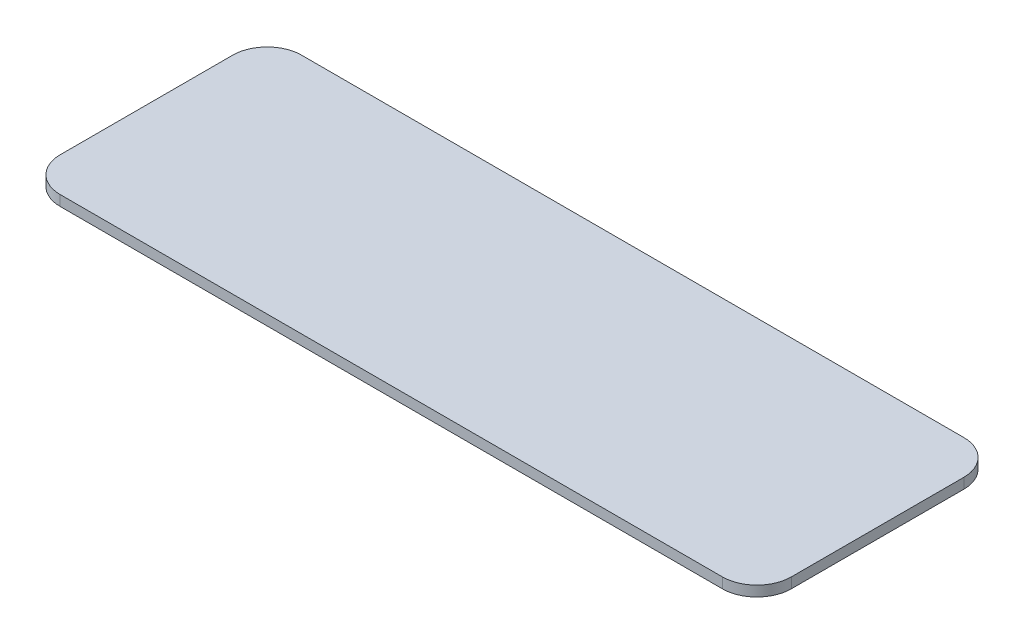
SolidWorks part; units mm, degrees
ref_plane "Front Plane" through (0, 0, 0) normal (0, 0, 1) x (1, 0, 0)
ref_plane "Top Plane" through (0, 0, 0) normal (0, 1, 0) x (1, 0, 0)
ref_plane "Right Plane" through (0, 0, 0) normal (1, 0, 0) x (0, 0, -1)
sketch "Sketch1" plane through (0, 0, 0) normal (0, 1, 0) x (1, 0, 0)
  line L1 (-106, -35) -> (106, -35)
  line L2 (-106, -35) -> (-106, 35)
  line L3 (-106, 35) -> (106, 35)
  line L4 (106, -35) -> (106, 35)
  line L5 (-106, -35) -> (106, 35) construction
  line L6 (-106, 35) -> (106, -35) construction
  point P0 (0, 0)
  dimension "D1" = 70
  dimension "D2" = 212
extrude "Boss-Extrude1" add sketch "Sketch1" along normal blind 3
fillet "Fillet1" radius 10 4 edges at (-106, 1.5, 35) (106, 1.5, 35) (106, 1.5, -35) (-106, 1.5, -35)
